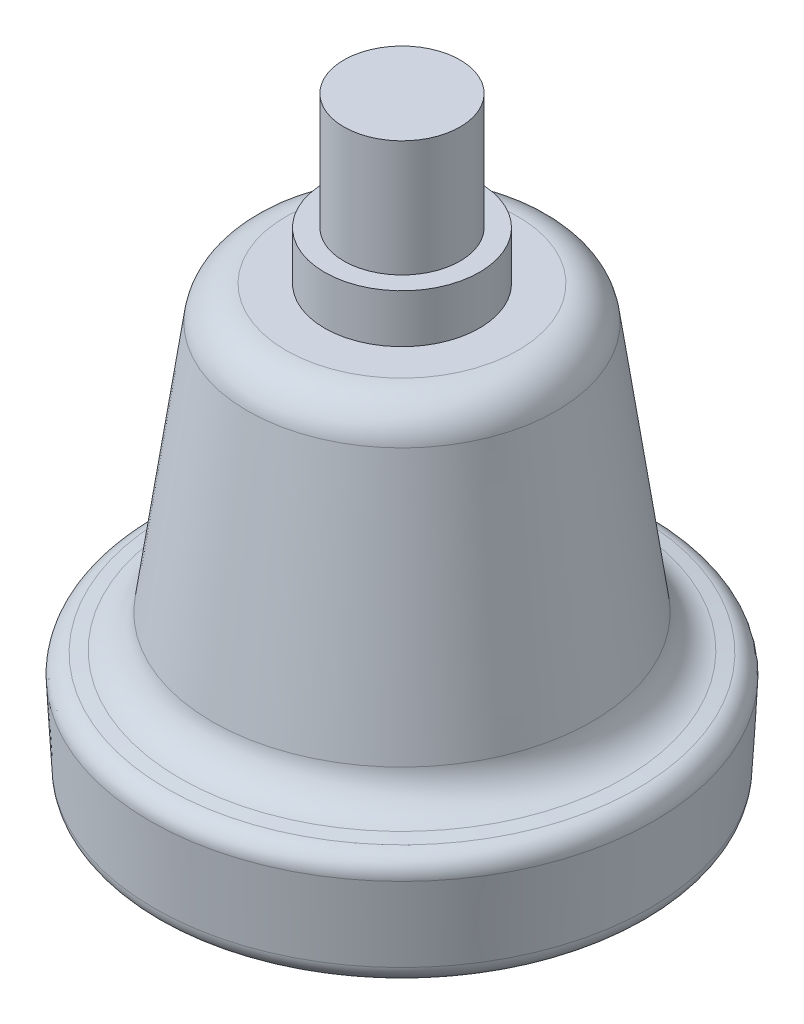
SolidWorks part; units mm, degrees
ref_plane "Plan de face" through (0, 0, 0) normal (0, 0, 1) x (1, 0, 0)
ref_plane "Plan de dessus" through (0, 0, 0) normal (0, 1, 0) x (1, 0, 0)
ref_plane "Plan de droite" through (0, 0, 0) normal (1, 0, 0) x (0, 0, -1)
sketch "Esquisse1" plane through (0, 0, 0) normal (1, 0, 0) x (0, 0, -1)
  line L0 (8, -5) -> (8, 0)
  line L1 (0, -50) -> (23.5807, -50)
  line L2 (8, 0) -> (6, 0)
  line L3 (6, 0) -> (6, 12)
  line L4 (6, 12) -> (0, 12)
  line L5 (0, 55) -> (0, -55) construction
  line L6 (55, 0) -> (-55, 0) construction
  line L7 (11.9775, -5) -> (8, -5)
  line L9 (25.578, -48.1047) -> (25.9973, -40.1047)
  line L10 (24.3129, -38.0246) -> (22.9234, -37.8046)
  line L11 (19.5881, -34.4105) -> (15.9386, -8.4433)
  line L12 (0, 12) -> (0, -50)
  arc A0 (15.9386, -8.4433) -> (11.9775, -5) centre (11.9775, -9) ccw
  arc A1 (25.9973, -40.1047) -> (24.3129, -38.0246) centre (24, -40) ccw
  arc A2 (23.5807, -50) -> (25.578, -48.1047) centre (23.5807, -48) ccw
  arc A3 (22.9234, -37.8046) -> (19.5881, -34.4105) centre (23.5491, -33.8538) cw
  point P20 (26.0915, -38.3063)
  point P26 (20, -37.3415)
  dimension "D9" = 2
  dimension "D10" = 4
  dimension "D1" = 6
  dimension "D2" = 12
  dimension "D3" = 5
  dimension "D4" = 8
  dimension "D5" = 3
  dimension "D6" = 8
  dimension "D7" = 20
  dimension "D8" = 8
  dimension "D11" = 50
  dimension "D12" = 24
  dimension "D13" = 9
revolve "Révolution1" add sketch "Esquisse1" angle 360 about L12
